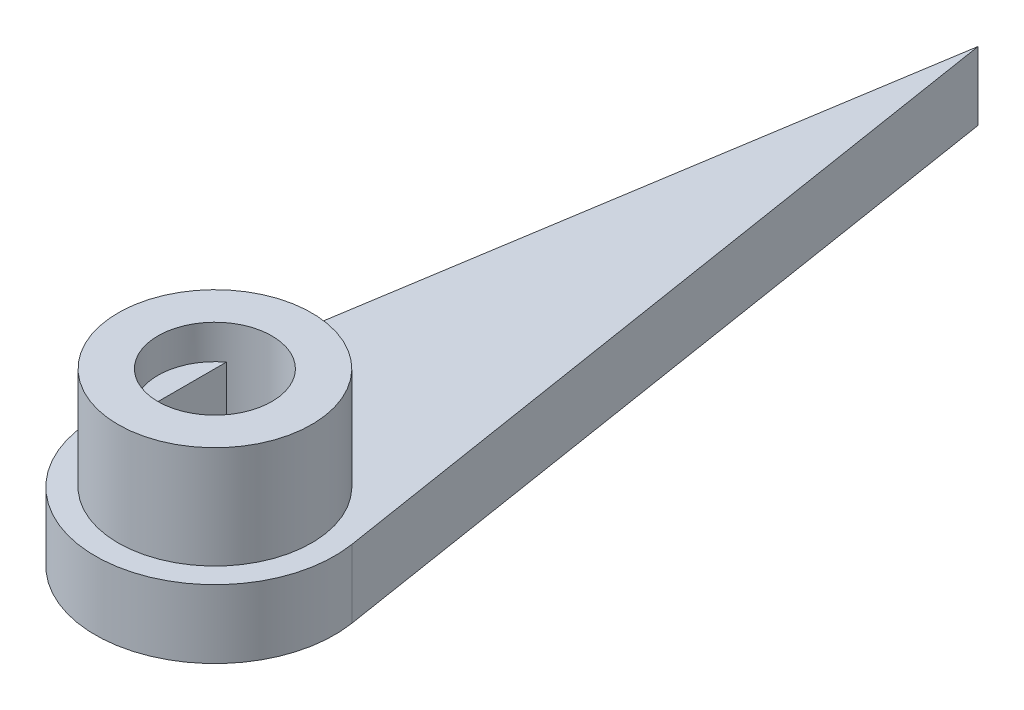
SolidWorks part; units mm, degrees
ref_plane "Front Plane" through (0, 0, 0) normal (0, 0, 1) x (1, 0, 0)
ref_plane "Top Plane" through (0, 0, 0) normal (0, 1, 0) x (1, 0, 0)
ref_plane "Right Plane" through (0, 0, 0) normal (1, 0, 0) x (0, 0, -1)
sketch "Sketch5" plane through (0, 0, 0) normal (0, 1, 0) x (1, 0, 0)
  circle A0 centre (0, 0) radius 4.25
  dimension "D1" = 8.5
extrude "Boss-Extrude3" add sketch "Sketch5" along normal blind 7.5
sketch "Sketch7" plane through (0, 7.5, 0) normal (0, 1, 0) x (1, 0, 0)
  circle A0 centre (0, 0) radius 2.5
  dimension "D1" = 5
extrude "Cut-Extrude2" cut sketch "Sketch7" against normal blind 1.5
sketch "Sketch8" plane through (0, 6, 0) normal (0, 1, 0) x (1, 0, 0)
  line L0 (-1.5, -2) -> (-1.5, 2)
  line L1 (1.5, 2) -> (1.5, -2)
  circle A0 centre (0, 0) radius 2.5 construction
  circle A1 centre (0, 0) radius 2.5 construction
  arc A2 (-1.5, -2) -> (1.5, -2) centre (0, 0) ccw
  arc A3 (1.5, 2) -> (-1.5, 2) centre (0, 0) ccw
  dimension "D1" = 3
extrude "Cut-Extrude3" cut sketch "Sketch8" against normal blind 6
sketch "Sketch9" plane through (0, 0, 0) normal (0, 1, 0) x (1, 0, 0)
  line L0 (-5.1851, 0.8228) -> (0, 33.5)
  line L1 (0, 33.5) -> (5.1851, 0.8228)
  line L2 (1.5, -2) -> (1.5, 2) construction
  line L3 (-1.5, 2) -> (-1.5, -2) construction
  line L4 (1.5, -2) -> (1.5, 2)
  line L5 (-1.5, 2) -> (-1.5, -2)
  arc A0 (-1.5, -2) -> (1.5, -2) centre (0, 0) ccw construction
  arc A1 (1.5, 2) -> (-1.5, 2) centre (0, 0) ccw construction
  circle A2 centre (0, 0) radius 5.25
  circle A3 centre (0, 0) radius 5.25
  arc A4 (-1.5, -2) -> (1.5, -2) centre (0, 0) ccw
  arc A5 (1.5, 2) -> (-1.5, 2) centre (0, 0) ccw
  point P3 (5.8038, 28.6541)
  point P6 (0, 39.5931)
  point P7 (0, 0)
  point P12 (0, 33.5)
  dimension "D1" = 1
extrude "Boss-Extrude4" add sketch "Sketch9" along normal blind 3 contours A3 L1 L0 | A3 A5 L4 A4 L5
